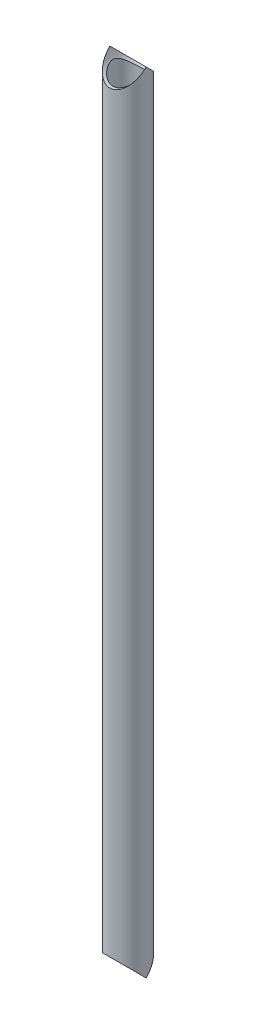
SolidWorks part; units mm, degrees
material "6061-T6 (SS)"
ref_plane "Front Plane" through (0, 0, 0) normal (0, 0, 1) x (1, 0, 0)
ref_plane "Top Plane" through (0, 0, 0) normal (0, 1, 0) x (1, 0, 0)
ref_plane "Right Plane" through (0, 0, 0) normal (1, 0, 0) x (0, 0, -1)
sketch "Sketch1" plane through (0, 0, 0) normal (0, 1, 0) x (1, 0, 0)
  circle A0 centre (0, 0) radius 21.082
  circle A1 centre (0, 0) radius 17.526
  dimension "D1" = 42.164
  dimension "D2" = 35.052
extrude "Boss-Extrude1" add sketch "Sketch1" along normal blind 914.4
sketch "Sketch2" plane through (0, 0, 0) normal (0, 0, 1) x (1, 0, 0)
  line L0 (21.082, 914.4) -> (-21.082, 914.4) construction
  circle A0 centre (0, 0) radius 21.082
  circle A1 centre (0, 914.4) radius 21.082
  dimension "D1" = 42.164
  dimension "D2" = 42.164
extrude "Cut-Extrude1" cut sketch "Sketch2" against normal through all both and the other way through all
